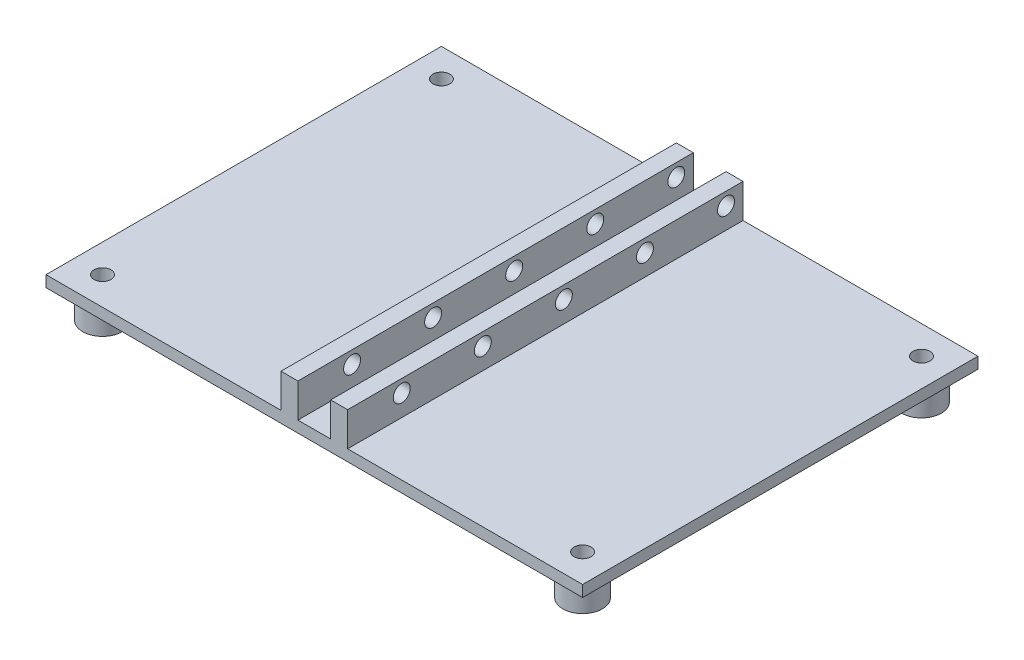
SolidWorks part; units mm, degrees
ref_plane "前视基准面" through (0, 0, 0) normal (0, 0, 1) x (1, 0, 0)
ref_plane "上视基准面" through (0, 0, 0) normal (0, 1, 0) x (1, 0, 0)
ref_plane "右视基准面" through (0, 0, 0) normal (1, 0, 0) x (0, 0, -1)
other "Configuration Table"
sketch "草图1" plane through (0, 0, 0) normal (0, 1, 0) x (1, 0, 0)
  line L0 (-47.5, 35) -> (47.5, 35)
  line L1 (-42.5, 30) -> (42.5, 30) construction
  line L2 (-42.5, 30) -> (-42.5, -30) construction
  line L3 (-42.5, -30) -> (42.5, -30) construction
  line L4 (42.5, 30) -> (42.5, -30) construction
  line L5 (-42.5, 30) -> (42.5, -30) construction
  line L6 (-42.5, -30) -> (42.5, 30) construction
  line L7 (47.5, 35) -> (47.5, -35)
  line L8 (-47.5, -35) -> (47.5, -35)
  line L9 (-47.5, 35) -> (-47.5, -35)
  circle A1 centre (-42.5, 30) radius 1.5
  circle A2 centre (42.5, 30) radius 1.5
  circle A3 centre (-42.5, -30) radius 1.5
  circle A4 centre (42.5, -30) radius 1.5
  point P0 (0, 0)
  dimension "D4" = 2
  dimension "D1" = 85
  dimension "D2" = 60
  dimension "D3" = 5
extrude "凸台-拉伸1" add sketch "草图1" along normal blind 2
sketch "草图2" plane through (0, 2, 0) normal (0, 1, 0) x (1, 0, 0)
  line L0 (0, -39.9468) -> (0, 41.0986) construction
  line L1 (-2.9, -35) -> (-2.9, 35)
  line L2 (-47.5, -35) -> (47.5, -35) construction
  line L3 (47.5, 35) -> (-47.5, 35) construction
  line L4 (-5.9, -35) -> (-5.9, 35)
  line L5 (5.9, -35) -> (5.9, 35)
  line L6 (2.9, -35) -> (2.9, 35)
  line L7 (-5.9, -35) -> (-2.9, -35)
  line L8 (2.9, -35) -> (5.9, -35)
  line L9 (5.9, 35) -> (2.9, 35)
  line L10 (-2.9, 35) -> (-5.9, 35)
  dimension "D1" = 2.9
  dimension "D2" = 3
extrude "凸台-拉伸2" add sketch "草图2" along normal blind 6
sketch "草图3" plane through (-5.9, 0, 0) normal (-1, 0, 0) x (0, 0, 1)
  line L1 (-35, 2) -> (35, 2) construction
  circle A0 centre (-31.9859, 5.75) radius 1.5
  circle A1 centre (-17.6359, 5.75) radius 1.5
  circle A2 centre (-3.2859, 5.75) radius 1.5
  circle A3 centre (11.0641, 5.75) radius 1.5
  circle A4 centre (25.4141, 5.75) radius 1.5
  dimension "D1" = 3.75
  dimension "D2" = 4
  dimension "D3" = 2
extrude "切除-拉伸1" cut sketch "草图3" against normal through all
sketch "草图4" plane through (0, 0, 0) normal (0, -1, 0) x (1, 0, 0)
  circle A25 centre (-42.5, 30) radius 1.5
  circle A26 centre (42.5, 30) radius 1.5
  circle A27 centre (42.5, -30) radius 1.5
  circle A28 centre (-42.5, -30) radius 1.5
  circle A29 centre (-42.5, -30) radius 3.5
  circle A30 centre (-42.5, 30) radius 3.5
  circle A31 centre (42.5, 30) radius 3.5
  circle A32 centre (42.5, -30) radius 3.5
  dimension "D1" = 2
extrude "凸台-拉伸3" add sketch "草图4" along normal blind 5
